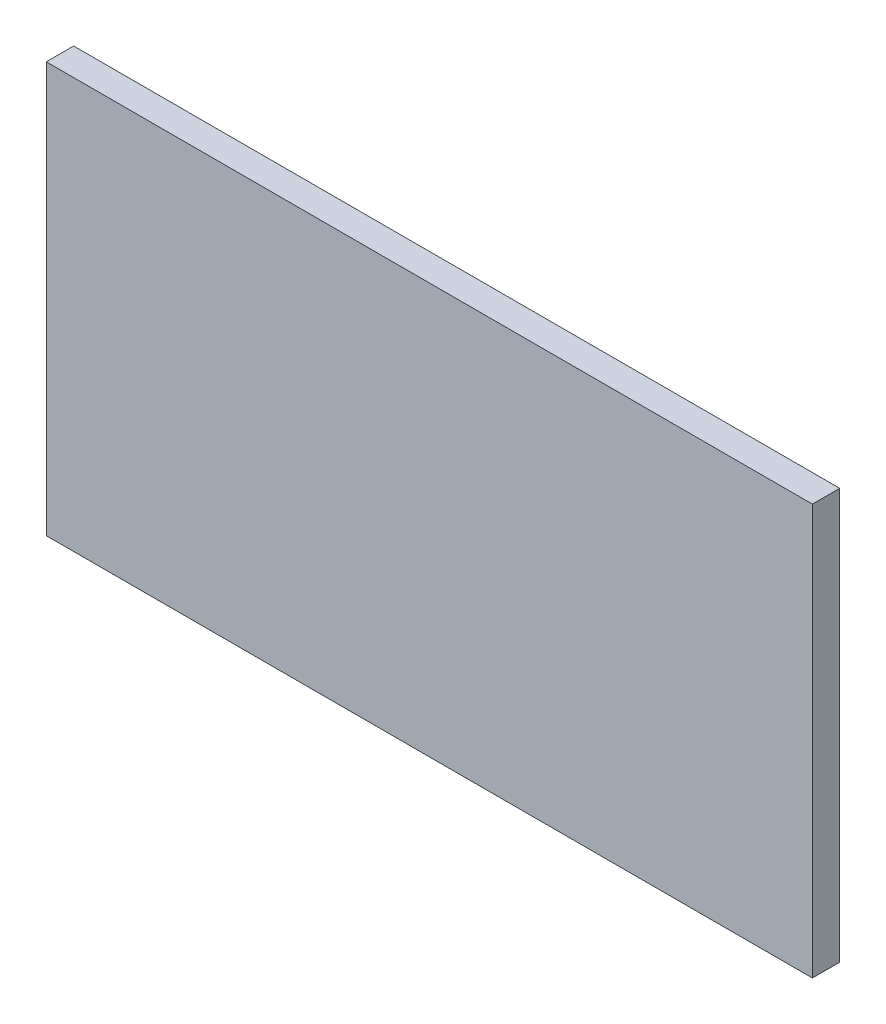
SolidWorks part; units mm, degrees
ref_plane "Front Plane" through (0, 0, 0) normal (0, 0, 1) x (1, 0, 0)
ref_plane "Top Plane" through (0, 0, 0) normal (0, 1, 0) x (1, 0, 0)
ref_plane "Right Plane" through (0, 0, 0) normal (1, 0, 0) x (0, 0, -1)
sketch "Sketch1" plane through (0, 0, 0) normal (0, 0, 1) x (1, 0, 0)
  line L1 (-88.9, 47.625) -> (88.9, 47.625)
  line L2 (-88.9, 47.625) -> (-88.9, -47.625)
  line L3 (-88.9, -47.625) -> (88.9, -47.625)
  line L4 (88.9, 47.625) -> (88.9, -47.625)
  line L5 (-88.9, 47.625) -> (88.9, -47.625) construction
  line L6 (-88.9, -47.625) -> (88.9, 47.625) construction
  point P0 (0, 0)
  dimension "D1" = 95.25
  dimension "D2" = 177.8
extrude "Boss-Extrude1" add sketch "Sketch1" along normal blind 6.35
